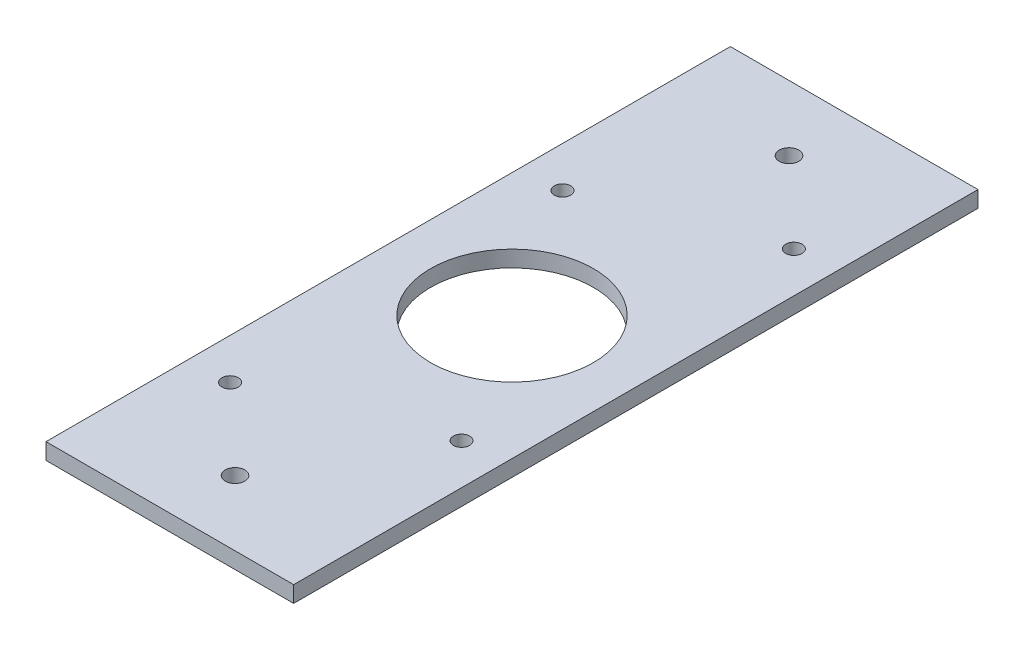
SolidWorks part; units mm, degrees
material "1060 Alloy"
ref_plane "Front Plane" through (0, 0, 0) normal (0, 0, 1) x (1, 0, 0)
ref_plane "Top Plane" through (0, 0, 0) normal (0, 1, 0) x (1, 0, 0)
ref_plane "Right Plane" through (0, 0, 0) normal (1, 0, 0) x (0, 0, -1)
sketch "Sketch1" plane through (0, 0, 0) normal (0, 1, 0) x (1, 0, 0)
  line L0 (-69.0262, -6.3906) -> (6.9738, -6.3906) construction
  line L1 (-69.0262, -111.3906) -> (6.9738, -111.3906)
  line L2 (-69.0262, -111.3906) -> (-69.0262, 98.6094)
  line L3 (-69.0262, 98.6094) -> (6.9738, 98.6094)
  line L4 (6.9738, -111.3906) -> (6.9738, 98.6094)
  line L5 (-69.0262, -111.3906) -> (6.9738, 98.6094) construction
  line L6 (-69.0262, 98.6094) -> (6.9738, -111.3906) construction
  circle A0 centre (-31.0262, 78.6094) radius 3
  circle A1 centre (-31.0262, -91.3906) radius 3
  circle A2 centre (-56.5262, 34.6094) radius 2.5
  circle A3 centre (-5.5262, 54.6094) radius 2.5
  circle A4 centre (-56.5262, -67.3906) radius 2.5
  circle A5 centre (-5.5262, -47.3906) radius 2.5
  circle A6 centre (-31.0262, -6.3906) radius 25
  point P0 (-31.0262, -6.3906)
  dimension "D4" = 6
  dimension "D5" = 5
  dimension "D6" = 5
  dimension "D7" = 5
  dimension "D8" = 5
  dimension "D1" = 76
  dimension "D2" = 210
  dimension "D3" = 20
  dimension "D9" = 44
  dimension "D10" = 64
  dimension "D11" = 51
  dimension "D12" = 20
  dimension "D13" = 146
  dimension "D14" = 166
  dimension "D15" = 12.5
  dimension "D16" = 38
extrude "Boss-Extrude1" add sketch "Sketch1" along normal blind 5
